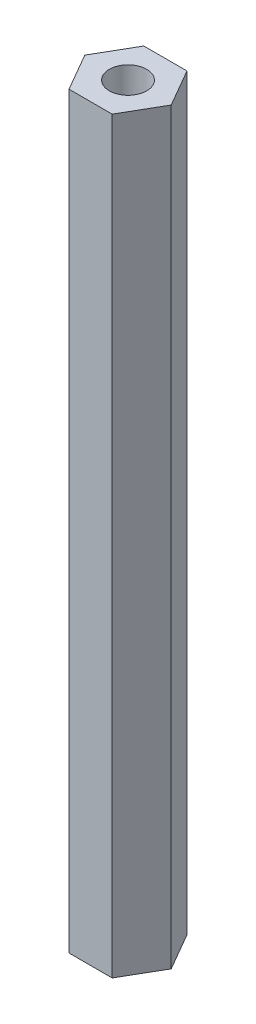
SolidWorks part; units mm, degrees
material "6061-T6 (SS)"
ref_plane "Front Plane" through (0, 0, 0) normal (0, 0, 1) x (1, 0, 0)
ref_plane "Top Plane" through (0, 0, 0) normal (0, 1, 0) x (1, 0, 0)
ref_plane "Right Plane" through (0, 0, 0) normal (1, 0, 0) x (0, 0, -1)
sketch "Sketch1" plane through (0, 0, 0) normal (0, 1, 0) x (1, 0, 0)
  line L1 (3.6662, -6.35) -> (7.3323, 0)
  line L2 (7.3323, 0) -> (3.6662, 6.35)
  line L3 (3.6662, 6.35) -> (-3.6662, 6.35)
  line L4 (-3.6662, 6.35) -> (-7.3323, 0)
  line L5 (-7.3323, 0) -> (-3.6662, -6.35)
  line L6 (-3.6662, -6.35) -> (3.6662, -6.35)
  circle A0 centre (0, 0) radius 6.35 construction
  circle A1 centre (0, 0) radius 3.175
  point P10 (-5.4993, -3.175)
  point P11 (5.4993, 3.175)
  dimension "D2" = 6.35
  dimension "D1" = 12.7
extrude "Boss-Extrude1" add sketch "Sketch1" along normal mid plane 127
